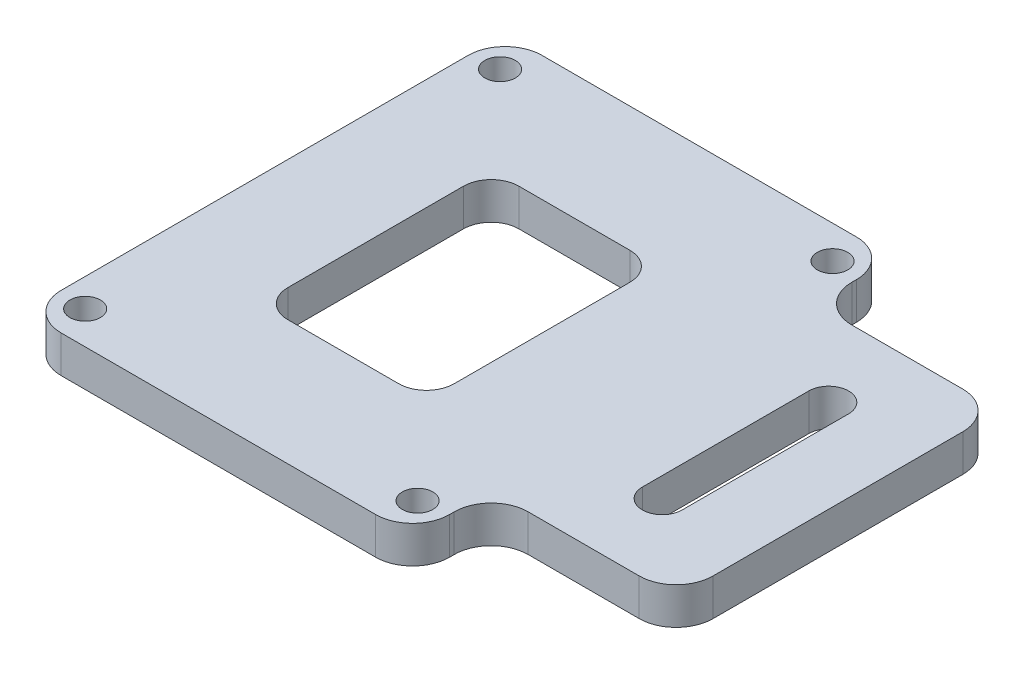
SolidWorks part; units mm, degrees
ref_plane "前视基准面" through (0, 0, 0) normal (0, 0, 1) x (1, 0, 0)
ref_plane "上视基准面" through (0, 0, 0) normal (0, 1, 0) x (1, 0, 0)
ref_plane "右视基准面" through (0, 0, 0) normal (1, 0, 0) x (0, 0, -1)
sketch "Sketch1" plane through (0, 0, 0) normal (0, 1, 0) x (1, 0, 0)
  line L1 (-21, -26) -> (21, -26)
  line L2 (-21, -26) -> (-21, 26)
  line L3 (-21, 26) -> (21, 26)
  line L4 (21, -26) -> (21, 26)
  line L5 (-21, -26) -> (21, 26) construction
  line L6 (-21, 26) -> (21, -26) construction
  point P0 (0, 0)
  dimension "D1" = 42
  dimension "D2" = 52
extrude "Boss-Extrude1" add sketch "Sketch1" along normal blind 4
sketch "Sketch2" plane through (0, 4, 0) normal (0, 1, 0) x (1, 0, 0)
  line L1 (-17.975, -22.4375) -> (17.975, -22.4375) construction
  line L2 (-17.975, -22.4375) -> (-17.975, 22.4375) construction
  line L3 (-17.975, 22.4375) -> (17.975, 22.4375) construction
  line L4 (17.975, -22.4375) -> (17.975, 22.4375) construction
  line L5 (-17.975, -22.4375) -> (17.975, 22.4375) construction
  line L6 (-17.975, 22.4375) -> (17.975, -22.4375) construction
  circle A0 centre (-17.975, 22.4375) radius 1.65
  circle A1 centre (17.975, 22.4375) radius 1.65
  circle A2 centre (17.975, -22.4375) radius 1.65
  circle A3 centre (-17.975, -22.4375) radius 1.65
  point P0 (0, 0)
  dimension "D1" = 3.3
  dimension "D2" = 35.95
  dimension "D3" = 44.875
extrude "Cut-Extrude1" cut sketch "Sketch2" against normal through all both and the other way through all
sketch "Sketch3" plane through (0, 4, 0) normal (0, 1, 0) x (1, 0, 0)
  line L0 (21, -26) -> (21, 26) construction
  line L1 (41, 17.5) -> (21, 17.5)
  line L2 (41, 17.5) -> (41, -17.5)
  line L3 (41, -17.5) -> (21, -17.5)
  line L4 (21, 17.5) -> (21, -17.5)
  line L5 (41, 17.5) -> (21, -17.5) construction
  line L6 (41, -17.5) -> (21, 17.5) construction
  point P0 (31, 0)
  point P7 (0, 0)
  dimension "D1" = 20
  dimension "D2" = 35
extrude "Boss-Extrude2" add sketch "Sketch3" against normal blind 4
fillet "Fillet1" radius 4 8 edges at (21, 2, -26) (21, 2, 26) (-21, 2, 26) (-21, 2, -26) (21, 2, -17.5) (21, 2, 17.5) (41, 2, 17.5) (41, 2, -17.5)
sketch "Sketch4" plane through (0, 4, 0) normal (0, 1, 0) x (1, 0, 0)
  line L0 (31, 17.5) -> (31, -17.5) construction
  line L1 (37, 17.5) -> (25, 17.5) construction
  line L2 (25, -17.5) -> (37, -17.5) construction
  line L3 (31, -9) -> (31, 9) construction
  line L4 (28.85, -9) -> (28.85, 9)
  line L5 (33.15, -9) -> (33.15, 9)
  arc A0 (28.85, -9) -> (33.15, -9) centre (31, -9) ccw
  arc A1 (33.15, 9) -> (28.85, 9) centre (31, 9) ccw
  point P8 (31, 0)
  dimension "D1" = 4.3
  dimension "D2" = 18
extrude "Cut-Extrude2" cut sketch "Sketch4" against normal through all both and the other way through all
sketch "Sketch5" plane through (0, 4, 0) normal (0, 1, 0) x (1, 0, 0)
  line L1 (-9, -12.5) -> (9, -12.5)
  line L2 (-9, -12.5) -> (-9, 12.5)
  line L3 (-9, 12.5) -> (9, 12.5)
  line L4 (9, -12.5) -> (9, 12.5)
  line L5 (-9, -12.5) -> (9, 12.5) construction
  line L6 (-9, 12.5) -> (9, -12.5) construction
  point P0 (0, 0)
  dimension "D1" = 18
  dimension "D2" = 25
extrude "Cut-Extrude3" cut sketch "Sketch5" against normal through all both and the other way through all
fillet "Fillet2" radius 3 4 edges at (9, 2, 12.5) (-9, 2, 12.5) (-9, 2, -12.5) (9, 2, -12.5)
